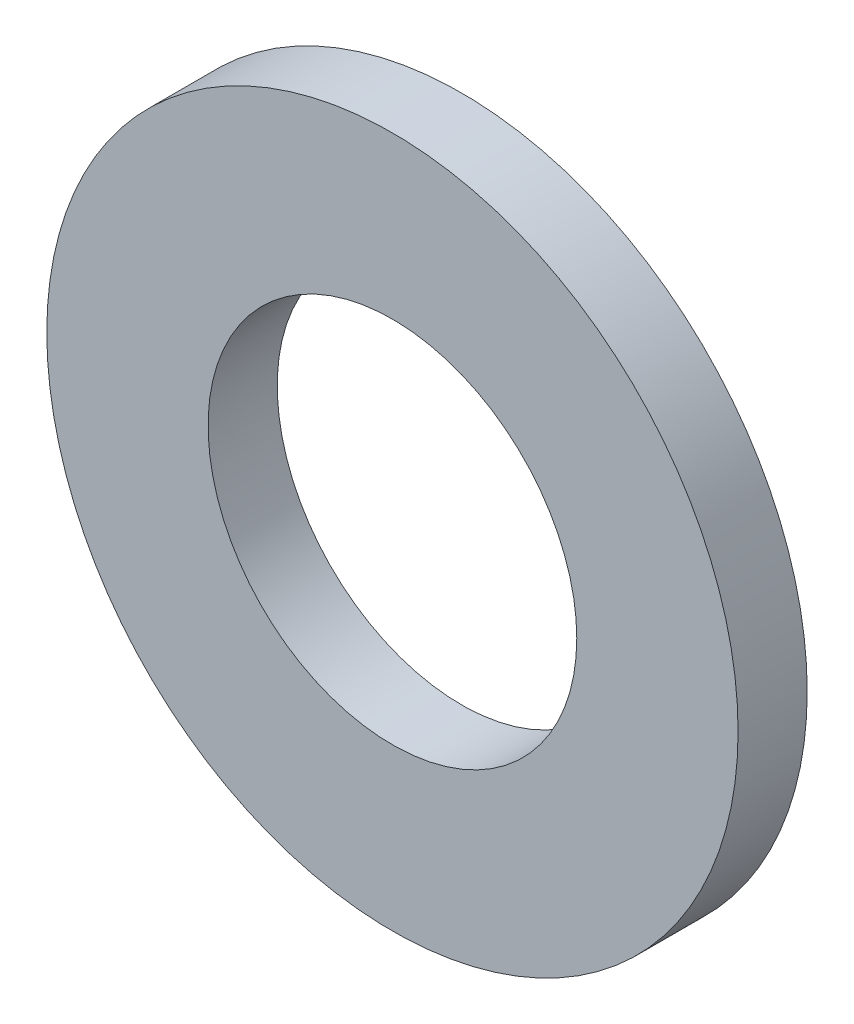
SolidWorks part; units mm, degrees
ref_plane "Front Plane" through (0, 0, 0) normal (0, 0, 1) x (1, 0, 0)
ref_plane "Top Plane" through (0, 0, 0) normal (0, 1, 0) x (1, 0, 0)
ref_plane "Right Plane" through (0, 0, 0) normal (1, 0, 0) x (0, 0, -1)
sketch "Sketch1" plane through (0, 0, 0) normal (0, 0, 1) x (1, 0, 0)
  circle A0 centre (0, 0) radius 3
  circle A1 centre (0, 0) radius 1.6
  point P5 (0, -3)
  dimension "OD" = 6
  dimension "ID" = 3.2
sketch "Sketch2" plane through (0, 0, 0) normal (1, 0, 0) x (0, 0, -1)
  line L0 (-0.3, 0) -> (0.3, 0) construction
  point P0 (-0.3, -3)
  point P4 (0, 0)
  point P6 (0.3, -3)
  dimension "Thickness Range" = 0.6
sketch "Sketch3" plane through (0, 0, 0) normal (0, 0, 1) x (1, 0, 0)
  circle A0 centre (0, 0) radius 3 construction
  circle A1 centre (0, 0) radius 1.6 construction
  circle A2 centre (0, 0) radius 3
  circle A3 centre (0, 0) radius 1.6
extrude "Boss-Extrude1" add sketch "Sketch3" along normal up to vertex (0.3 mm away) and the other way up to vertex (0.3 mm away) up to point (0, -3, 0.3) other way up to point (0, -3, -0.3)
